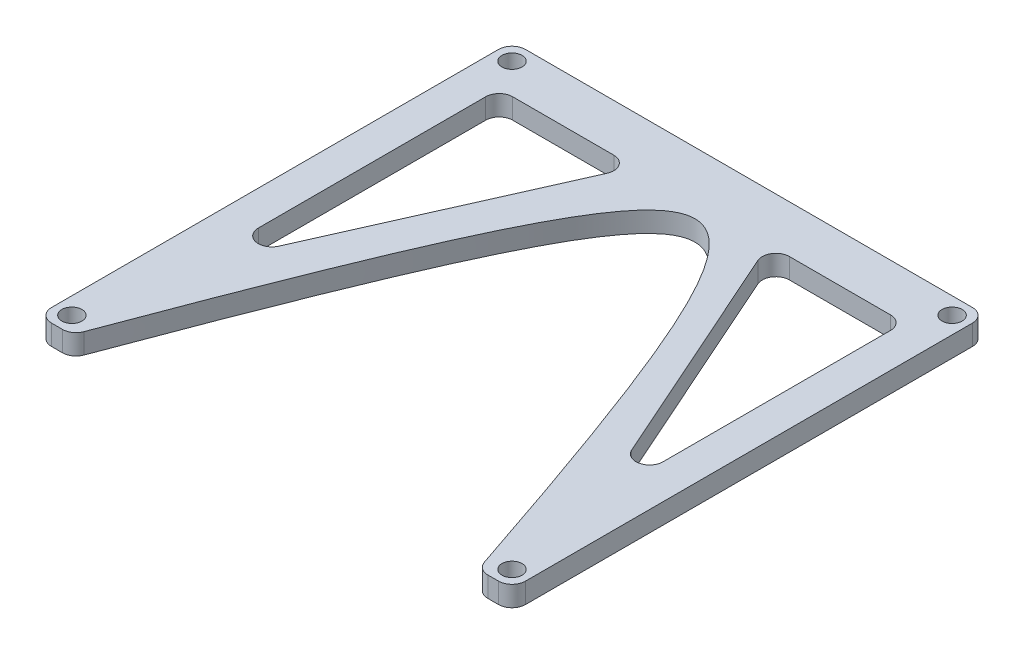
SolidWorks part; units mm, degrees
ref_plane "Front Plane" through (0, 0, 0) normal (0, 0, 1) x (1, 0, 0)
ref_plane "Top Plane" through (0, 0, 0) normal (0, 1, 0) x (1, 0, 0)
ref_plane "Right Plane" through (0, 0, 0) normal (1, 0, 0) x (0, 0, -1)
sketch "Sketch2" plane through (0, 0, 0) normal (0, 1, 0) x (1, 0, 0)
  line L0 (-30, -35) -> (-35, -35)
  line L1 (-35, 35) -> (35, 35)
  line L2 (-35, 35) -> (-35, -35)
  line L3 (-35, -35) -> (35, -35) construction
  line L4 (35, 35) -> (35, -35)
  line L5 (-35, 35) -> (35, -35) construction
  line L6 (-35, -35) -> (35, 35) construction
  line L7 (35, -35) -> (30, -35)
  conic Q0 (-30, -35) -> (30, -35) control (1.6025, 50.0815) rho 0.71534
  point P0 (0, 0)
  dimension "D3" = 60
  dimension "D1" = 70
  dimension "D2" = 70
  dimension "D4" = 5
extrude "Boss-Extrude1" add sketch "Sketch2" along normal blind 3
sketch "Sketch3" plane through (0, 3, 0) normal (0, 1, 0) x (1, 0, 0)
  line L0 (-35, 35) -> (-35, -35) construction
  line L1 (35, 35) -> (-35, 35) construction
  circle A0 centre (-32.5, 32.5) radius 1.4881
  circle A1 centre (32.5, 32.5) radius 1.4881
  circle A2 centre (32.5, -32.5) radius 1.4881
  circle A3 centre (-32.5, -32.5) radius 1.4881
  dimension "D1" = 2.9763
  dimension "D2" = 2.5
  dimension "D3" = 2.5
  dimension "D4" = 2
extrude "Cut-Extrude1" cut sketch "Sketch3" against normal through all
fillet "Fillet1" radius 2 6 edges at (35, 1.5, 35) (30, 1.5, 35) (-30, 1.5, 35) (-35, 1.5, 35) (-35, 1.5, -35) (35, 1.5, -35)
sketch "Sketch4" plane through (0, 3, 0) normal (0, 1, 0) x (1, 0, 0)
  line L0 (-29.8916, -17) -> (-29.8916, 28)
  line L1 (-29.8916, 28) -> (-9.8916, 28)
  line L2 (-9.8916, 28) -> (-29.8916, -17)
  line L3 (0, 49.3751) -> (0, -57.6391) construction
  line L4 (29.8916, -17) -> (29.8916, 28)
  line L5 (29.8916, 28) -> (9.8916, 28)
  line L6 (9.8916, 28) -> (29.8916, -17)
  line L7 (33, 35) -> (-33, 35) construction
  dimension "D1" = 45
  dimension "D2" = 20
  dimension "D3" = 7
extrude "Cut-Extrude2" cut sketch "Sketch4" against normal through all
fillet "Fillet2" radius 2 6 edges at (29.8916, 1.5, -28) (9.8916, 1.5, -28) (29.8916, 1.5, 17) (-29.8916, 1.5, 17) (-29.8916, 1.5, -28) (-9.8916, 1.5, -28)
